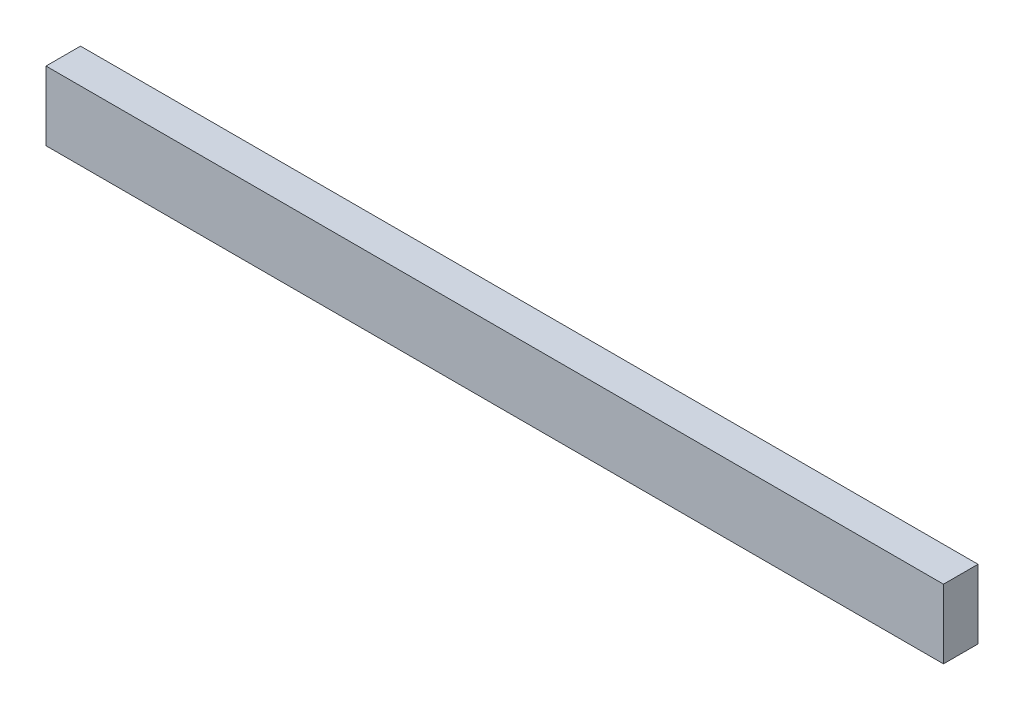
SolidWorks part; units mm, degrees
ref_plane "Front Plane" through (0, 0, 0) normal (0, 0, 1) x (1, 0, 0)
ref_plane "Top Plane" through (0, 0, 0) normal (0, 1, 0) x (1, 0, 0)
ref_plane "Right Plane" through (0, 0, 0) normal (1, 0, 0) x (0, 0, -1)
sketch "Sketch1" plane through (0, 0, 0) normal (0, 0, 1) x (1, 0, 0)
  line L1 (-130, -10) -> (130, -10)
  line L2 (-130, -10) -> (-130, 10)
  line L3 (-130, 10) -> (130, 10)
  line L4 (130, -10) -> (130, 10)
  line L5 (-130, -10) -> (130, 10) construction
  line L6 (-130, 10) -> (130, -10) construction
  point P0 (0, 0)
  dimension "D1" = 20
  dimension "D2" = 260
extrude "Boss-Extrude1" add sketch "Sketch1" against normal blind 10
